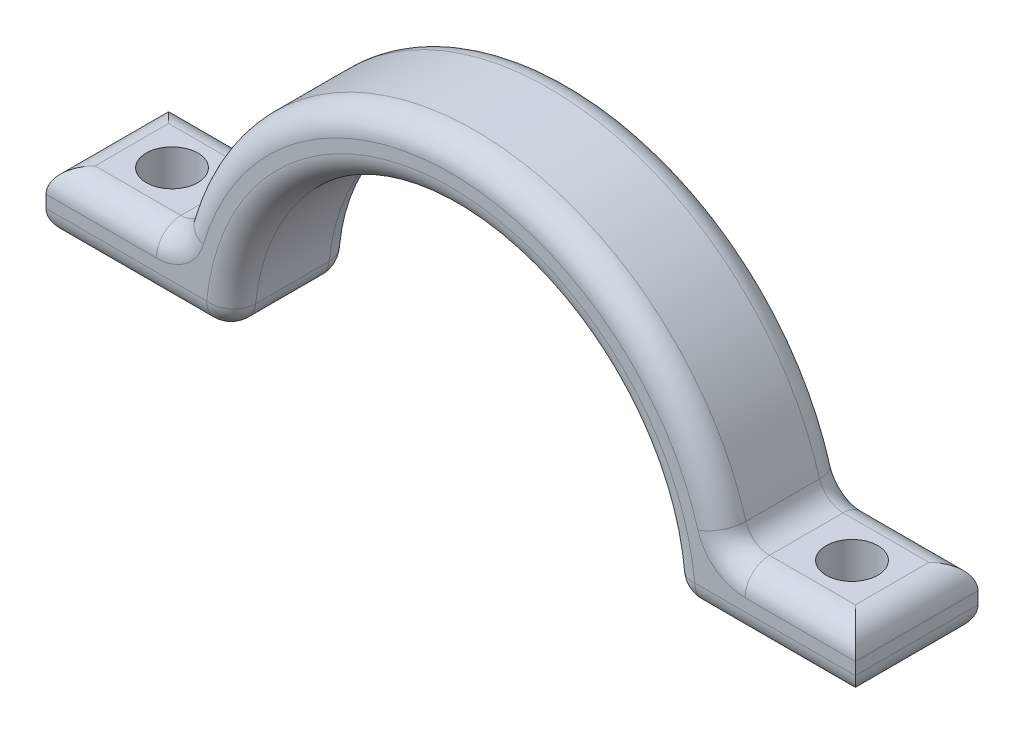
SolidWorks part; units mm, degrees
ref_plane "Front Plane" through (0, 0, 0) normal (0, 0, 1) x (1, 0, 0)
ref_plane "Top Plane" through (0, 0, 0) normal (0, 1, 0) x (1, 0, 0)
ref_plane "Right Plane" through (0, 0, 0) normal (1, 0, 0) x (0, 0, -1)
sketch "Sketch1" plane through (0, 0, 0) normal (0, 0, 1) x (1, 0, 0)
  line L0 (-23, 0) -> (-18, 0)
  line L2 (18, 0) -> (23, 0)
  arc A0 (18, 0) -> (-18, 0) centre (0, 0) ccw
  arc A1 (23, 0) -> (-23, 0) centre (0, 0) ccw
  circle A2 centre (0, 0) radius 23 construction
  circle A3 centre (0, 0) radius 18 construction
  dimension "D1" = 36
  dimension "D2" = 5
extrude "Boss-Extrude1" add sketch "Sketch1" along normal blind 10
ref_plane "Plane1" through (-23, 0, 0) normal (-1, 0, 0) x (0, 0, 1)
sketch "Sketch2" plane through (-23, 0, 0) normal (-1, 0, 0) x (0, 0, 1)
  line L1 (10, 0) -> (0, 0)
  line L2 (10, 0) -> (10, 5)
  line L3 (10, 5) -> (0, 5)
  line L4 (0, 0) -> (0, 5)
  line L5 (10, 0) -> (0, 5) construction
  line L6 (10, 5) -> (0, 0) construction
  point P4 (5, 2.5)
  dimension "D1" = 5
  dimension "D2" = 10
extrude "Boss-Extrude2" add sketch "Sketch2" along normal blind 10 and the other way up to surface
sketch "Sketch3" plane through (0, 5, 0) normal (0, 1, 0) x (1, 0, 0)
  line L0 (-27.725, -10) -> (-27.725, 0) construction
  line L1 (-22.4499, -10) -> (-33, -10) construction
  line L2 (-22.4499, 0) -> (-33, 0) construction
  circle A0 centre (-27.725, -5) radius 2.1
  dimension "D1" = 4.2
extrude "Cut-Extrude1" cut sketch "Sketch3" against normal blind 10
mirror "Mirror1" about plane through (0, 0, 0) normal (1, 0, 0) of "Boss-Extrude2", "Cut-Extrude1"
fillet "Fillet1" radius 2 20 edges at (27.725, 5, 10) (27.725, 5, 0) (-27.725, 5, 10) (-27.725, 5, 0) (25.5, 0, 10) (25.5, 0, 0) (-25.5, 0, 0) (-25.5, 0, 10) (0, 23, 10) (0, 23, 0) (0, 18, 0) (0, 18, 10) (22.4499, 5, 5) (33, 5, 5) (33, 0, 5) (18, 0, 5) (-22.4499, 5, 5) (-33, 5, 5) (-18, 0, 5) (-33, 0, 5)
